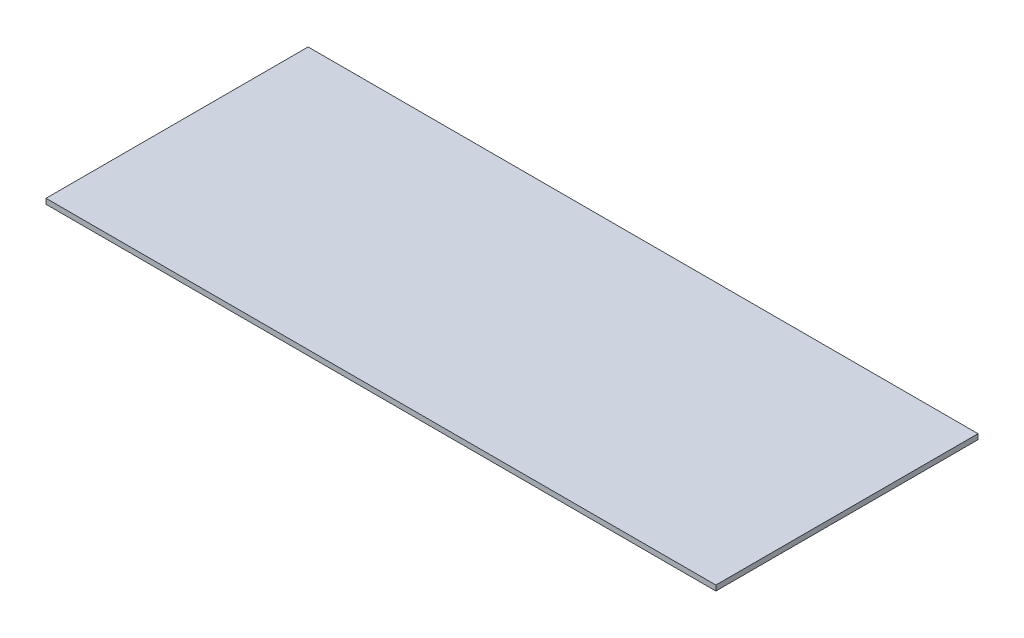
SolidWorks part; units mm, degrees
material "ABS"
ref_plane "Front Plane" through (0, 0, 0) normal (0, 0, 1) x (1, 0, 0)
ref_plane "Top Plane" through (0, 0, 0) normal (0, 1, 0) x (1, 0, 0)
ref_plane "Right Plane" through (0, 0, 0) normal (1, 0, 0) x (0, 0, -1)
sketch "Sketch1" plane through (0, 0, 0) normal (0, 1, 0) x (1, 0, 0)
  line L1 (0, 0) -> (2300, 0)
  line L2 (0, 0) -> (0, 900)
  line L3 (0, 900) -> (2300, 900)
  line L4 (2300, 0) -> (2300, 900)
  dimension "D1" = 900
  dimension "D2" = 2300
extrude "Boss-Extrude1" add sketch "Sketch1" along normal blind 18
